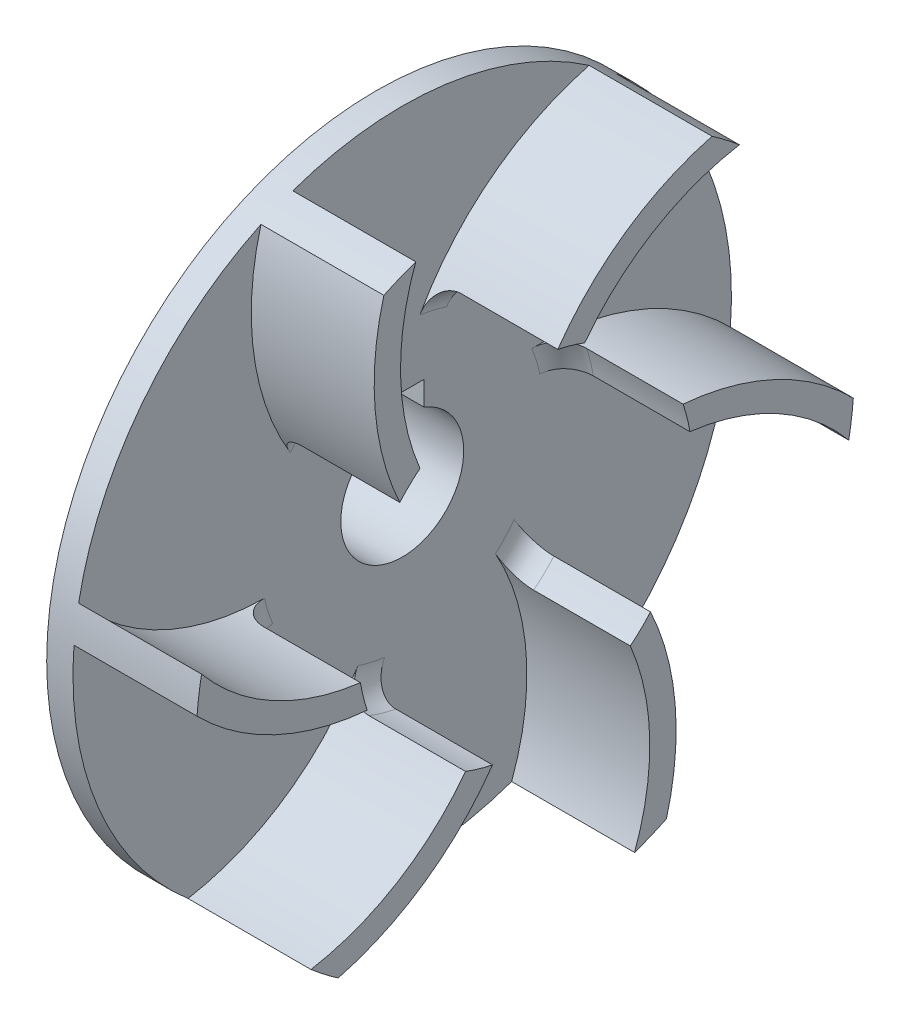
SolidWorks part; units mm, degrees
ref_plane "Front Plane" through (0, 0, 0) normal (0, 0, 1) x (1, 0, 0)
ref_plane "Top Plane" through (0, 0, 0) normal (0, 1, 0) x (1, 0, 0)
ref_plane "Right Plane" through (0, 0, 0) normal (1, 0, 0) x (0, 0, -1)
sketch "Sketch1" plane through (0, 0, 0) normal (0, 0, 1) x (1, 0, 0)
  line L0 (-91.9007, 0) -> (86.9312, 0) construction
  line L1 (0, 7) -> (0, 12.5)
  line L2 (0, 12.5) -> (16, 12.5)
  line L3 (16, 12.5) -> (16, 37.5)
  line L4 (16, 37.5) -> (19, 37.5)
  line L5 (19, 37.5) -> (19, 7)
  line L6 (19, 7) -> (0, 7)
  dimension "D1" = 25
  dimension "D2" = 16
  dimension "D3" = 3
  dimension "D4" = 14
  dimension "D5" = 75
revolve "Revolve1" add sketch "Sketch1" angle 360 about L0
fillet "Fillet1" radius 6 1 edges at (16, 0, 12.5)
sketch "Sketch2" plane through (19, 0, 0) normal (1, 0, 0) x (0, 0, -1)
  line L0 (-2.5, 6.5383) -> (-2.5, 9.3)
  line L1 (-2.5, 9.3) -> (2.5, 9.3)
  line L2 (2.5, 9.3) -> (2.5, 6.5383)
  circle A0 centre (0, 0) radius 7 construction
  arc A1 (-2.5, 6.5383) -> (2.5, 6.5383) centre (0, 0) ccw
  point P6 (0, 9.3)
  point P8 (0, 0)
  dimension "D1" = 16.3
  dimension "D2" = 5
extrude "Cut-Extrude1" cut sketch "Sketch2" against normal through all
sketch "Sketch3" plane through (19, 0, 0) normal (1, 0, 0) x (0, 0, -1)
  arc A0 (-36.8615, 6.8907) -> (-18.7617, -3) centre (-15.3287, 24.7888) ccw
  circle A1 centre (0, 0) radius 37.5 construction
  arc A2 (-37.3798, 3) -> (-17.9954, -6.0963) centre (-15.3287, 24.7888) ccw
  arc A3 (-18.7617, -3) -> (-17.9954, -6.0963) centre (0, 0) ccw
  circle A5 centre (0, 0) radius 37.5
  arc A6 (-36.8615, 6.8907) -> (-37.3798, 3) centre (0, 0) ccw
  point P7 (0, 0)
  point P8 (0, 0)
  dimension "D3" = 31
  dimension "D4" = 28
  dimension "D5" = 19
  dimension "D1" = 3
  dimension "D2" = 3
  dimension "D6" = 0
extrude "Boss-Extrude1" add sketch "Sketch3" along normal blind 14
fillet "Fillet2" radius 3 1 edges at (19, -4.5643, 18.4436)
pattern_circular "CirPattern1" count 6 over 360 about axis through (0, 0, 0) along (1, 0, 0) of "Fillet2", "Boss-Extrude1"
